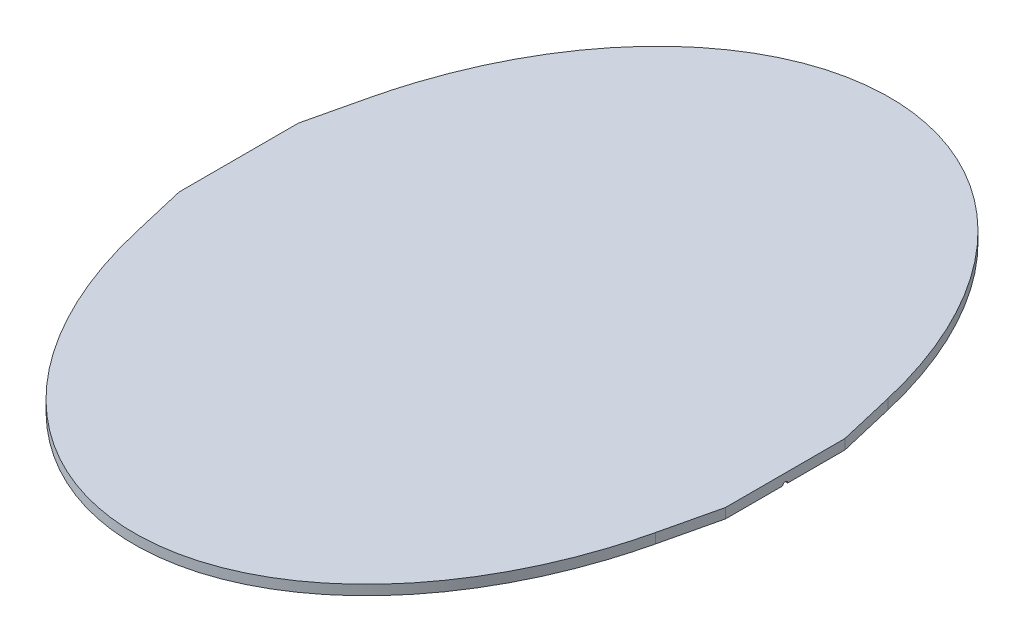
SolidWorks part; units mm, degrees
ref_plane "Front Plane" through (0, 0, 0) normal (0, 0, 1) x (1, 0, 0)
ref_plane "Top Plane" through (0, 0, 0) normal (0, 1, 0) x (1, 0, 0)
ref_plane "Right Plane" through (0, 0, 0) normal (1, 0, 0) x (0, 0, -1)
sketch "Sketch1" plane through (0, 0, 0) normal (0, 1, 0) x (1, 0, 0)
  ellipse E1 centre (0, 0) end of major axis (0, 380) minor radius 275
  dimension "D3" = 550
  dimension "D4" = 760
extrude "Boss-Extrude1" add sketch "Sketch1" along normal blind 10
sketch "Sketch2" plane through (0, 10, 0) normal (0, 1, 0) x (-1, 0, 0)
  line L0 (-261.6216, -117.0811) -> (-275, -60)
  line L1 (-275, -60) -> (-275, 0)
  line L2 (-275, -60) -> (-275, 60) construction
  line L3 (-275, 0) -> (-275, 60)
  line L4 (-275, 60) -> (-261.6216, 117.0811)
  line L5 (-261.6216, 117.0811) -> (-261.6216, -117.0811)
  line L6 (0, 520.3963) -> (0, -482.8995) construction
  line L7 (0, -520.2694) -> (0, 520.3963) construction
  line L8 (261.6216, 117.0811) -> (261.6216, -117.0811)
  line L9 (275, 60) -> (261.6216, 117.0811)
  line L10 (275, 0) -> (275, 60)
  line L11 (275, -60) -> (275, 0)
  line L12 (261.6216, -117.0811) -> (275, -60)
extrude "Boss-Extrude2" add sketch "Sketch2" against normal blind 10
sketch "Sketch3" plane through (275, 0, 0) normal (1, 0, 0) x (0, 0, -1)
  line L0 (-2.5, 0) -> (2.5, 0)
  arc A0 (2.5, 0) -> (-2.5, 0) centre (0, 0) ccw
  dimension "D1" = 5
extrude "Cut-Extrude1" cut sketch "Sketch3" against normal blind 10
sketch "Sketch4" plane through (-275, 0, 0) normal (-1, 0, 0) x (0, 0, 1)
  line L0 (-60, 0) -> (60, 0) construction
  line L1 (-2.5, 0) -> (2.5, 0)
  circle A0 centre (0, 0) radius 2.5 construction
  arc A1 (2.5, 0) -> (-2.5, 0) centre (0, 0) ccw
  dimension "D1" = 5
extrude "Cut-Extrude2" cut sketch "Sketch4" against normal blind 10
